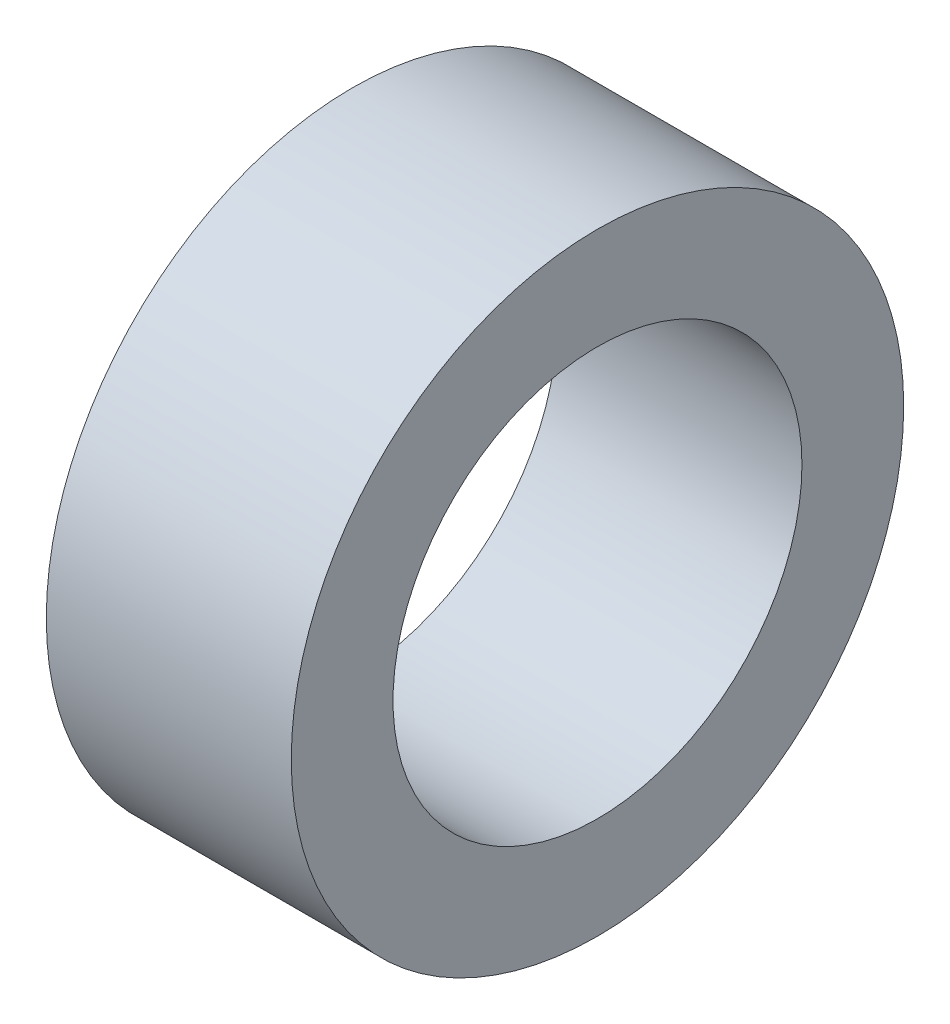
SolidWorks part; units mm, degrees
ref_plane "Front Plane" through (0, 0, 0) normal (0, 0, 1) x (1, 0, 0)
ref_plane "Top Plane" through (0, 0, 0) normal (0, 1, 0) x (1, 0, 0)
ref_plane "Right Plane" through (0, 0, 0) normal (1, 0, 0) x (0, 0, -1)
sketch "Sketch1" plane through (0, 0, 0) normal (1, 0, 0) x (0, 0, -1)
  circle A0 centre (0, 0) radius 2.65
  circle A1 centre (0, 0) radius 3.9688
  dimension "D1" = 5.3
  dimension "D2" = 7.9375
extrude "Boss-Extrude1" add sketch "Sketch1" along normal blind 3.175
